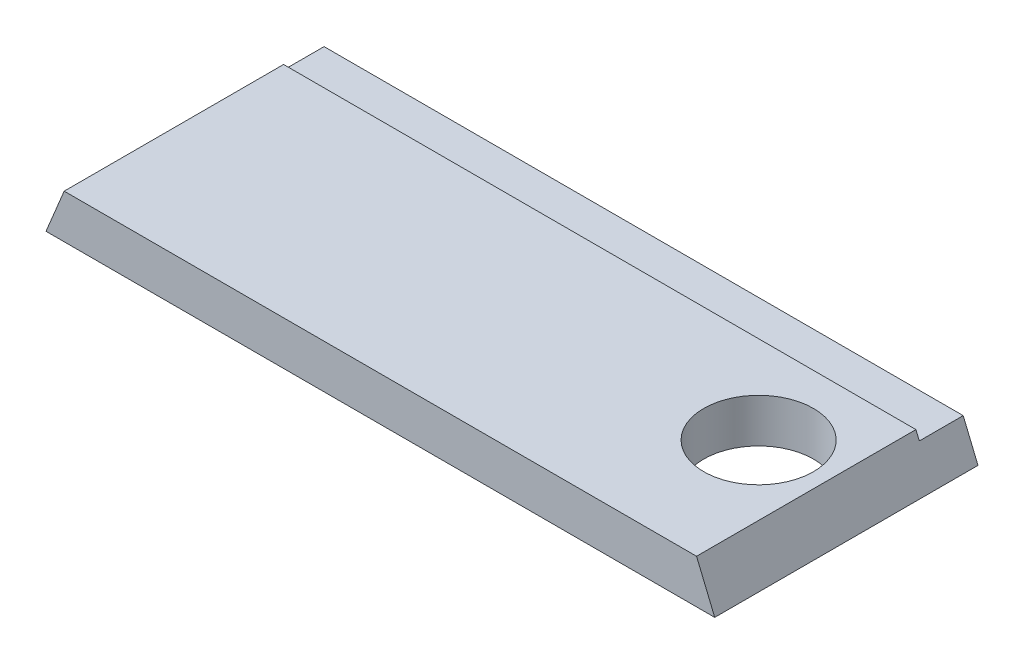
SolidWorks part; units mm, degrees
ref_plane "Front Plane" through (0, 0, 0) normal (0, 0, 1) x (1, 0, 0)
ref_plane "Top Plane" through (0, 0, 0) normal (0, 1, 0) x (1, 0, 0)
ref_plane "Right Plane" through (0, 0, 0) normal (1, 0, 0) x (0, 0, -1)
sketch "Sketch1" plane through (0, 0, 0) normal (0, 0, 1) x (1, 0, 0)
  line L0 (0, 0) -> (193.548, 0)
  line L1 (193.548, 0) -> (188.2875, 12.7)
  line L2 (188.2875, 12.7) -> (5.2605, 12.7)
  line L3 (5.2605, 12.7) -> (0, 0)
  dimension "D1" = 12.7
  dimension "D2" = 193.548
  dimension "D3" = 67.5
  dimension "D4" = 67.5
extrude "Boss-Extrude1" add sketch "Sketch1" along normal blind 76.2
sketch "Sketch2" plane through (0, 12.7, 0) normal (0, 1, 0) x (1, 0, 0)
  line L0 (193.548, -76.2) -> (193.548, 0) construction
  line L1 (193.548, -12.7) -> (0, -12.7)
  line L2 (193.548, -12.7) -> (193.548, 0)
  line L3 (193.548, 0) -> (0, 0)
  line L4 (0, -12.7) -> (0, 0)
  dimension "D1" = 12.7
extrude "Cut-Extrude1" cut sketch "Sketch2" against normal blind 2.3622
sketch "Sketch3" plane through (0, 0, 0) normal (0, -1, 0) x (1, 0, 0)
  line L0 (0, 76.2) -> (193.548, 76.2) construction
  line L1 (193.548, 76.2) -> (193.548, 0) construction
  circle A0 centre (168.148, 38.1) radius 15.875
  dimension "D1" = 31.75
  dimension "D2" = 38.1
  dimension "D3" = 25.4
extrude "Cut-Extrude2" cut sketch "Sketch3" against normal through all
